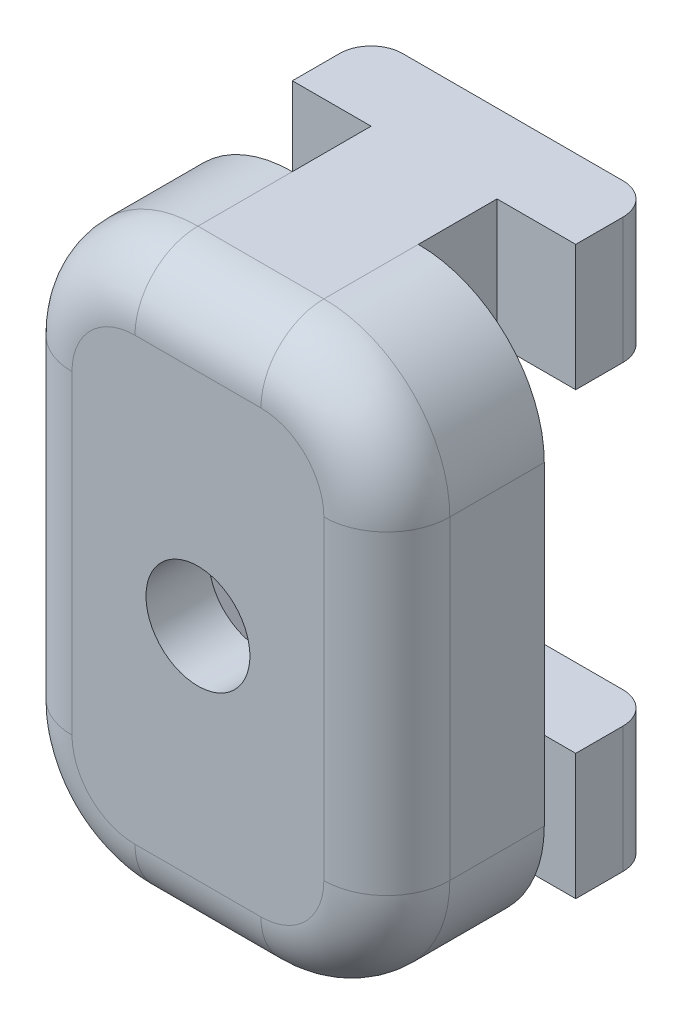
SolidWorks part; units mm, degrees
ref_plane "Plan de face" through (0, 0, 0) normal (0, 0, 1) x (1, 0, 0)
ref_plane "Plan de dessus" through (0, 0, 0) normal (0, 1, 0) x (1, 0, 0)
ref_plane "Plan de droite" through (0, 0, 0) normal (1, 0, 0) x (0, 0, -1)
sketch "Esquisse2" plane through (0, 0, 0) normal (0, 1, 0) x (1, 0, 0)
  line L1 (11.5687, 38.1282) -> (18.5687, 38.1282)
  line L2 (10.5687, 37.1282) -> (10.5687, 35.6282)
  line L3 (10.5687, 35.6282) -> (13.0687, 35.6282)
  line L4 (19.5687, 37.1282) -> (19.5687, 35.6282)
  line L7 (13.0687, 33.1282) -> (13.0687, 35.6282)
  line L9 (17.0687, 33.1282) -> (17.0687, 35.6282)
  line L10 (17.0687, 35.6282) -> (19.5687, 35.6282)
  line L11 (17.0687, 33.1282) -> (21.0687, 33.1282)
  line L12 (9.0687, 33.1282) -> (13.0687, 33.1282)
  line L13 (9.0687, 33.1282) -> (9.0687, 28.1282)
  line L14 (9.0687, 28.1282) -> (21.0687, 28.1282)
  line L15 (21.0687, 33.1282) -> (21.0687, 28.1282)
  arc A0 (18.5687, 38.1282) -> (19.5687, 37.1282) centre (18.5687, 37.1282) cw
  arc A1 (11.5687, 38.1282) -> (10.5687, 37.1282) centre (11.5687, 37.1282) ccw
  point P12 (15.0687, 38.1282)
  point P13 (15.0687, 28.1282)
  point P16 (19.5687, 38.1282)
  point P19 (10.5687, 38.1282)
  dimension "D4" = 1
  dimension "D1" = 9
  dimension "D2" = 2.5
  dimension "D3" = 4
  dimension "D5" = 2.5
  dimension "D6" = 12
  dimension "D7" = 5
extrude "Boss.-Extru.3" add sketch "Esquisse2" along normal blind 4
sketch "Esquisse3" plane through (0, 4, 0) normal (0, 1, 0) x (1, 0, 0)
  line L1 (9.0687, 33.1282) -> (21.0687, 33.1282)
  line L2 (9.0687, 33.1282) -> (9.0687, 28.1282)
  line L3 (9.0687, 28.1282) -> (21.0687, 28.1282)
  line L4 (21.0687, 33.1282) -> (21.0687, 28.1282)
extrude "Boss.-Extru.4" add sketch "Esquisse3" along normal blind 5
mirror "Symétrie1" about plane through (0, 9, 0) normal (0, 1, 0) of bodies 104
sketch "Esquisse4" plane through (0, 0, -33.1282) normal (0, 0, -1) x (-1, 0, 0)
  line L0 (-15.0687, 18) -> (-15.0687, 0) construction
  line L1 (-18.5687, 18) -> (-11.5687, 18) construction
  line L2 (-18.5687, 0) -> (-11.5687, 0) construction
  circle A0 centre (-15.0687, 9) radius 1.65
  dimension "D1" = 3.3
extrude "Enlèv. mat.-Extru.1" cut sketch "Esquisse4" against normal up to next
sketch "Esquisse5" plane through (0, 0, -33.1282) normal (0, 0, -1) x (-1, 0, 0)
  line L6 (-13.4233, 11.85) -> (-16.7142, 11.85)
  line L7 (-16.7142, 11.85) -> (-18.3596, 9)
  line L8 (-18.3596, 9) -> (-16.7142, 6.15)
  line L9 (-16.7142, 6.15) -> (-13.4233, 6.15)
  line L10 (-13.4233, 6.15) -> (-11.7778, 9)
  line L11 (-11.7778, 9) -> (-13.4233, 11.85)
  line L12 (-18.3596, 9) -> (-11.7778, 9) construction
  point P3 (-15.0687, 6.15)
  point P7 (-15.0687, 9)
  point P10 (-15.0687, 9)
  dimension "D1" = 5.7
  dimension "D2" = 120
  dimension "D3" = 5.7
extrude "Enlèv. mat.-Extru.2" cut sketch "Esquisse5" against normal blind 3
fillet "Congé1" radius 4 4 edges at (9.0687, 0, -30.6282) (9.0687, 18, -30.6282) (21.0687, 18, -30.6282) (21.0687, 0, -30.6282)
fillet "Congé2" radius 2 8 edges at (21.0687, 9, -28.1282) (19.8972, 1.1716, -28.1282) (15.0687, 0, -28.1282) (10.2403, 1.1716, -28.1282) (9.0687, 9, -28.1282) (10.2403, 16.8284, -28.1282) (15.0687, 18, -28.1282) (19.8972, 16.8284, -28.1282)
